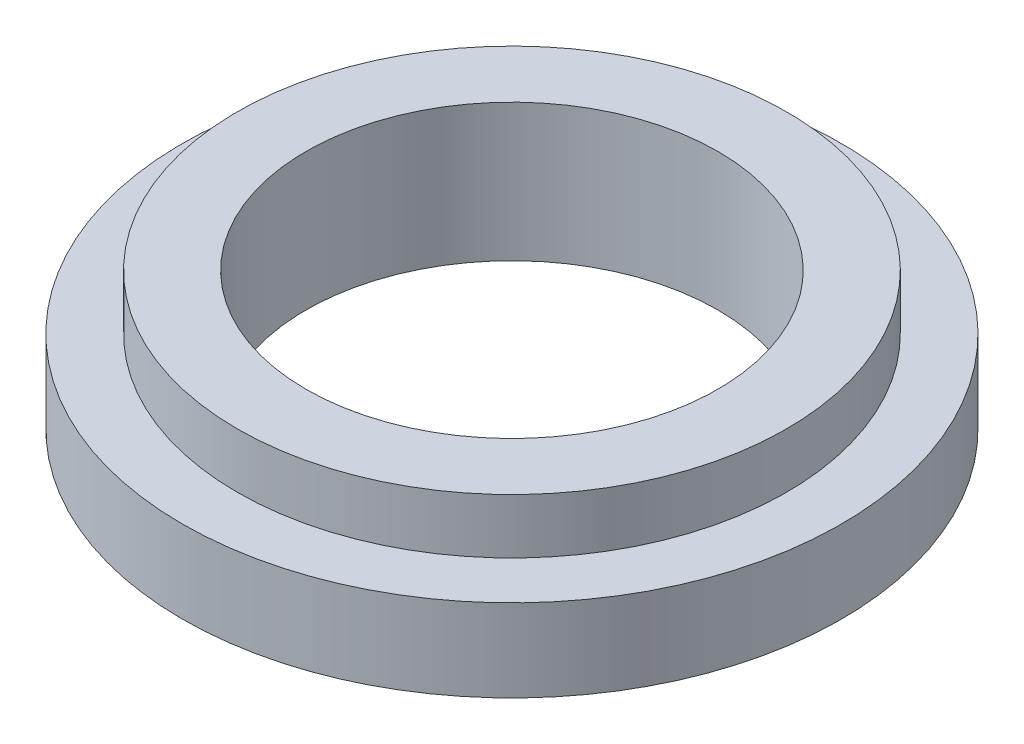
SolidWorks part; units mm, degrees
ref_plane "Front Plane" through (0, 0, 0) normal (0, 0, 1) x (1, 0, 0)
ref_plane "Top Plane" through (0, 0, 0) normal (0, 1, 0) x (1, 0, 0)
ref_plane "Right Plane" through (0, 0, 0) normal (1, 0, 0) x (0, 0, -1)
sketch "Sketch1" plane through (0, 0, 0) normal (0, 1, 0) x (1, 0, 0)
  circle A0 centre (0, 0) radius 12
  circle A1 centre (0, 0) radius 7.5
  dimension "D1" = 24
  dimension "D2" = 15
extrude "Boss-Extrude1" add sketch "Sketch1" along normal blind 3
sketch "Sketch2" plane through (0, 0, 0) normal (0, -1, 0) x (1, 0, 0)
  line L1 (0, 10) -> (-8.6603, 5) construction
  line L2 (-8.6603, 5) -> (-8.6603, -5) construction
  line L3 (-8.6603, -5) -> (0, -10) construction
  line L4 (0, -10) -> (8.6603, -5) construction
  line L5 (8.6603, -5) -> (8.6603, 5) construction
  line L6 (8.6603, 5) -> (0, 10) construction
  circle A0 centre (0, 0) radius 8.6603 construction
  circle A2 centre (0, 10) radius 1
  circle A3 centre (-8.6603, 5) radius 1
  circle A4 centre (-8.6603, -5) radius 1
  circle A5 centre (0, -10) radius 1
  circle A6 centre (8.6603, -5) radius 1
  circle A7 centre (8.6603, 5) radius 1
  dimension "D2" = 2
  dimension "D1" = 20
extrude "Cut-Extrude1" cut sketch "Sketch2" against normal blind 2.2
sketch "Sketch3" plane through (0, 3, 0) normal (0, 1, 0) x (1, 0, 0)
  circle A0 centre (0, 0) radius 10
  circle A1 centre (0, 0) radius 7.5
  circle A2 centre (0, 0) radius 7.5 construction
  dimension "D1" = 20
extrude "Boss-Extrude2" add sketch "Sketch3" along normal blind 2
